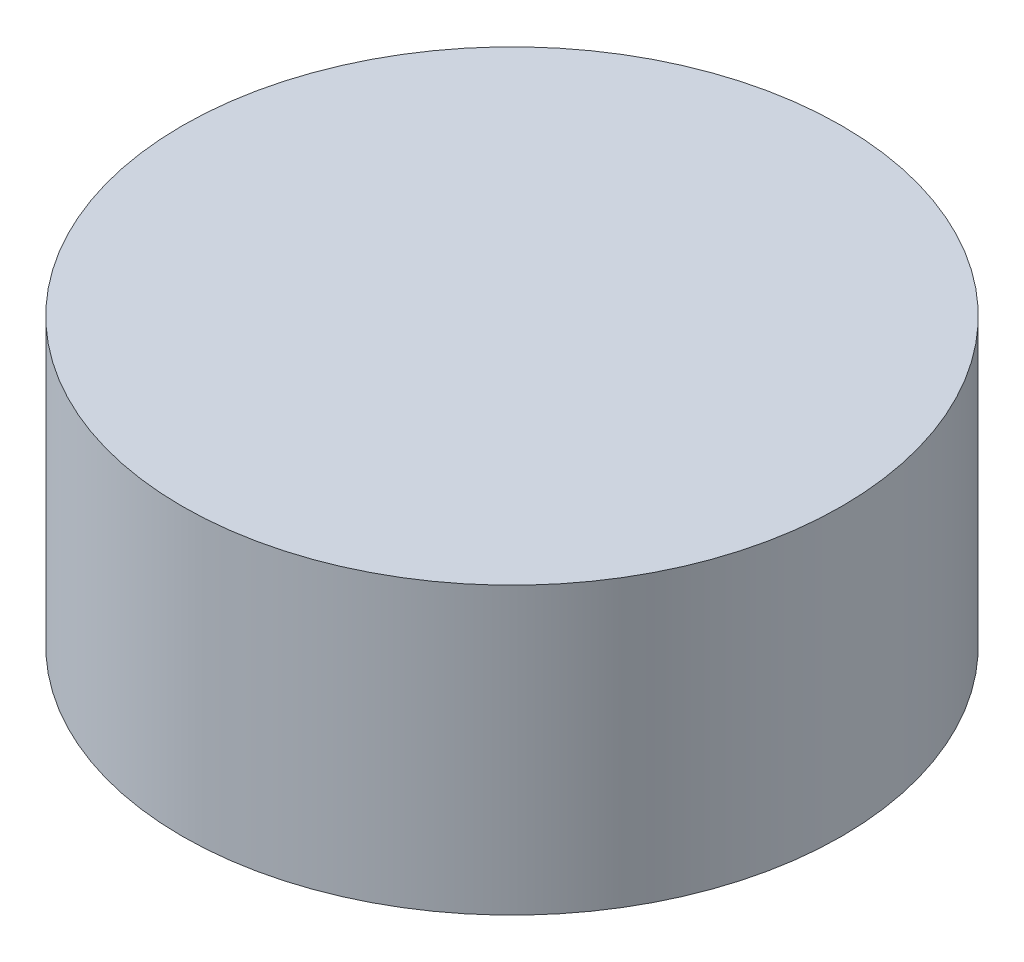
SolidWorks part; units mm, degrees
ref_plane "Front Plane" through (0, 0, 0) normal (0, 0, 1) x (1, 0, 0)
ref_plane "Top Plane" through (0, 0, 0) normal (0, 1, 0) x (1, 0, 0)
ref_plane "Right Plane" through (0, 0, 0) normal (1, 0, 0) x (0, 0, -1)
sketch "Sketch1" plane through (0, 0, 0) normal (0, 1, 0) x (1, 0, 0)
  circle A0 centre (0, 0) radius 9
  dimension "D1" = 18
extrude "Boss-Extrude1" add sketch "Sketch1" along normal blind 7.8
sketch "Sketch2" plane through (0, 7.8, 0) normal (0, 1, 0) x (1, 0, 0)
  circle A0 centre (0, 0) radius 1.35
  dimension "D1" = 2.7
extrude "Boss-Extrude2" [suppressed] add sketch "Sketch2" along normal blind 3
